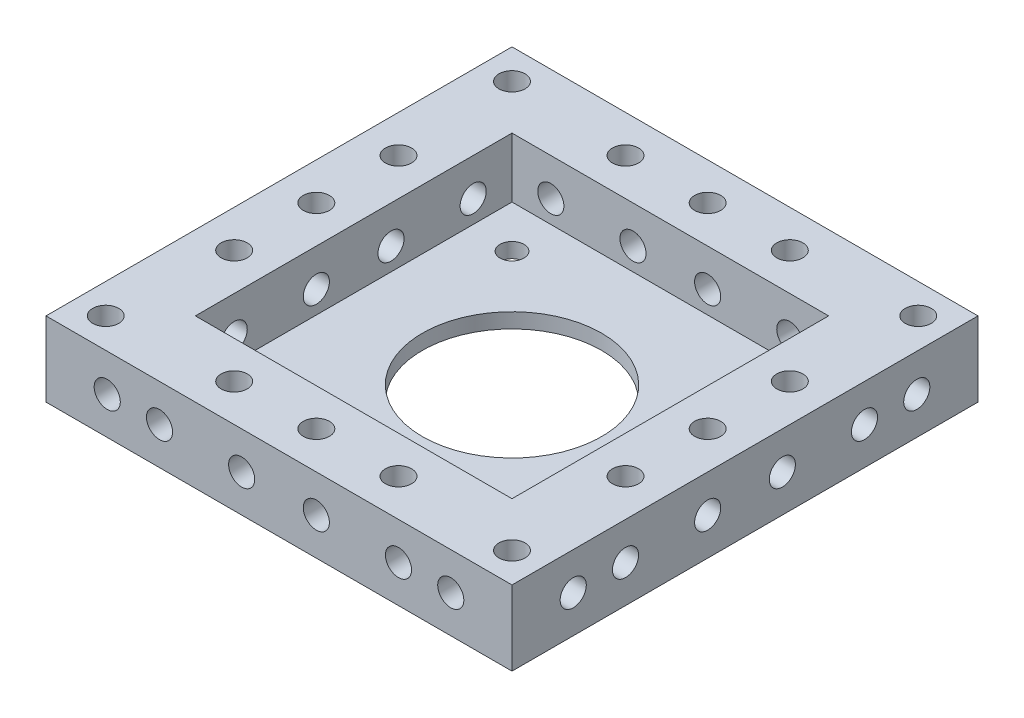
SolidWorks part; units mm, degrees
ref_plane "前视基准面" through (0, 0, 0) normal (0, 0, 1) x (1, 0, 0)
ref_plane "上视基准面" through (0, 0, 0) normal (0, 1, 0) x (1, 0, 0)
ref_plane "右视基准面" through (0, 0, 0) normal (1, 0, 0) x (0, 0, -1)
other "Configuration Table"
sketch "草图1" plane through (0, 0, 0) normal (0, 1, 0) x (1, 0, 0)
  line L1 (-21.2, 21.2) -> (21.2, 21.2)
  line L2 (-21.2, 21.2) -> (-21.2, -21.2)
  line L3 (-21.2, -21.2) -> (21.2, -21.2)
  line L4 (21.2, 21.2) -> (21.2, -21.2)
  line L5 (-21.2, 21.2) -> (21.2, -21.2) construction
  line L6 (-21.2, -21.2) -> (21.2, 21.2) construction
  point P0 (0, 0)
  dimension "D1" = 42.4
  dimension "D2" = 42.4
extrude "凸台-拉伸1" add sketch "草图1" along normal blind 2
sketch "草图2" plane through (0, 0, 0) normal (0, 1, 0) x (1, 0, 0)
  line L0 (-21.2, 21.2) -> (-21.2, -21.2) construction
  line L1 (-31.2, 31.2) -> (31.2, 31.2)
  line L2 (-31.2, 31.2) -> (-31.2, -31.2)
  line L3 (-31.2, -31.2) -> (31.2, -31.2)
  line L4 (31.2, 31.2) -> (31.2, -31.2)
  line L5 (-31.2, 31.2) -> (31.2, -31.2) construction
  line L6 (-31.2, -31.2) -> (31.2, 31.2) construction
  line L7 (21.2, 21.2) -> (-21.2, 21.2) construction
  line L12 (21.2, -21.2) -> (21.2, 21.2)
  line L13 (21.2, 21.2) -> (-21.2, 21.2)
  line L14 (-21.2, 21.2) -> (-21.2, -21.2)
  line L15 (-21.2, -21.2) -> (21.2, -21.2)
  line L16 (21.2, -21.2) -> (21.2, 21.2)
  line L17 (21.2, 21.2) -> (-21.2, 21.2)
  line L18 (-21.2, 21.2) -> (-21.2, -21.2)
  line L19 (-21.2, -21.2) -> (21.2, -21.2)
  point P0 (0, 0)
  dimension "D1" = 10
  dimension "D2" = 10
  dimension "D3" = 0
extrude "凸台-拉伸2" add sketch "草图2" along normal blind 10
sketch "草图5" plane through (0, 2, 0) normal (0, 1, 0) x (1, 0, 0)
  line L0 (0, 0) -> (-63.4453, 0) construction
  line L1 (0, 0) -> (0, 65.4768) construction
  circle A0 centre (-15.5, 15.5) radius 1.6
  circle A1 centre (15.5, 15.5) radius 1.6
  circle A2 centre (15.5, -15.5) radius 1.6
  circle A3 centre (-15.5, -15.5) radius 1.6
  circle A4 centre (0, 0) radius 12
  dimension "D1" = 3.2
  dimension "D4" = 24
  dimension "D2" = 15.5
  dimension "D3" = 15.5
extrude "切除-拉伸1" cut sketch "草图5" against normal up to next
sketch "草图7" plane through (-31.2, 0, 0) normal (-1, 0, 0) x (0, 0, 1)
  line L0 (0, 0) -> (0, 41.0076) construction
  line L1 (-31.2, 0) -> (31.2, 0) construction
  line L2 (-31.2, 10) -> (31.2, 10) construction
  circle A0 centre (-16, 5) radius 1.75
  circle A1 centre (16, 5) radius 1.75
  circle A2 centre (-23, 5) radius 1.75
  circle A3 centre (23, 5) radius 1.75
  circle A4 centre (-5, 5) radius 1.75
  circle A5 centre (5, 5) radius 1.75
  dimension "D1" = 3.5
  dimension "D3" = 5
  dimension "D4" = 3.5
  dimension "D5" = 5
  dimension "D6" = 23
  dimension "D7" = 3.5
  dimension "D8" = 5
  dimension "D9" = 5
  dimension "D2" = 16
extrude "切除-拉伸3" cut sketch "草图7" along normal up to surface (10 mm away)
pattern_circular "阵列(圆周)2" count 4 over 360 about axis through (0, 0, 0) along (0, 1, 0) of "切除-拉伸3"
sketch "草图8" plane through (0, 0, 31.2) normal (0, 0, 1) x (1, 0, 0)
  line L0 (0, -15.8102) -> (0, 25.1975) construction
  line L1 (-31.2, 10) -> (31.2, 10) construction
  circle A0 centre (-16, 5) radius 1.75
  circle A1 centre (16, 5) radius 1.75
  dimension "D1" = 3.5
  dimension "D3" = 5
  dimension "D2" = 16
extrude "切除-拉伸4" [suppressed] cut sketch "草图8" against normal through all
sketch "草图6" plane through (0, 10, 0) normal (0, 1, 0) x (1, 0, 0)
  line L0 (-31.2, 31.2) -> (-31.2, -31.2) construction
  line L1 (0, 0) -> (-39.2722, 39.2722) construction
  line L2 (0, 0) -> (0, 55.8586) construction
  line L3 (0, 0) -> (-64.3366, 0) construction
  line L5 (31.2, 31.2) -> (-31.2, 31.2) construction
  line L6 (-31.2, 31.2) -> (-31.2, -31.2) construction
  circle A0 centre (-27.2, 27.2) radius 1.75
  circle A6 centre (-26.2, 11) radius 1.75
  circle A7 centre (-26.2, 0) radius 1.75
  circle A8 centre (-11, 26.2) radius 1.75
  circle A9 centre (0, 26.2) radius 1.75
  circle A10 centre (11, 26.2) radius 1.75
  circle A11 centre (27.2, 27.2) radius 1.75
  circle A12 centre (26.2, 11) radius 1.75
  circle A13 centre (26.2, 0) radius 1.75
  circle A14 centre (26.2, -11) radius 1.75
  circle A15 centre (27.2, -27.2) radius 1.75
  circle A16 centre (11, -26.2) radius 1.75
  circle A17 centre (0, -26.2) radius 1.75
  circle A18 centre (-11, -26.2) radius 1.75
  circle A19 centre (-27.2, -27.2) radius 1.75
  circle A20 centre (-26.2, -11) radius 1.75
  point P46 (0, 0)
  dimension "D1" = 3.5
  dimension "D4" = 3.5
  dimension "D5" = 5
  dimension "D3" = 4
  dimension "D6" = 3.5
  dimension "D7" = 5
  dimension "D2" = 4
  dimension "D8" = 11
  dimension "D9" = 45
  dimension "D10" = 4
extrude "切除-拉伸2" cut sketch "草图6" against normal up to next
